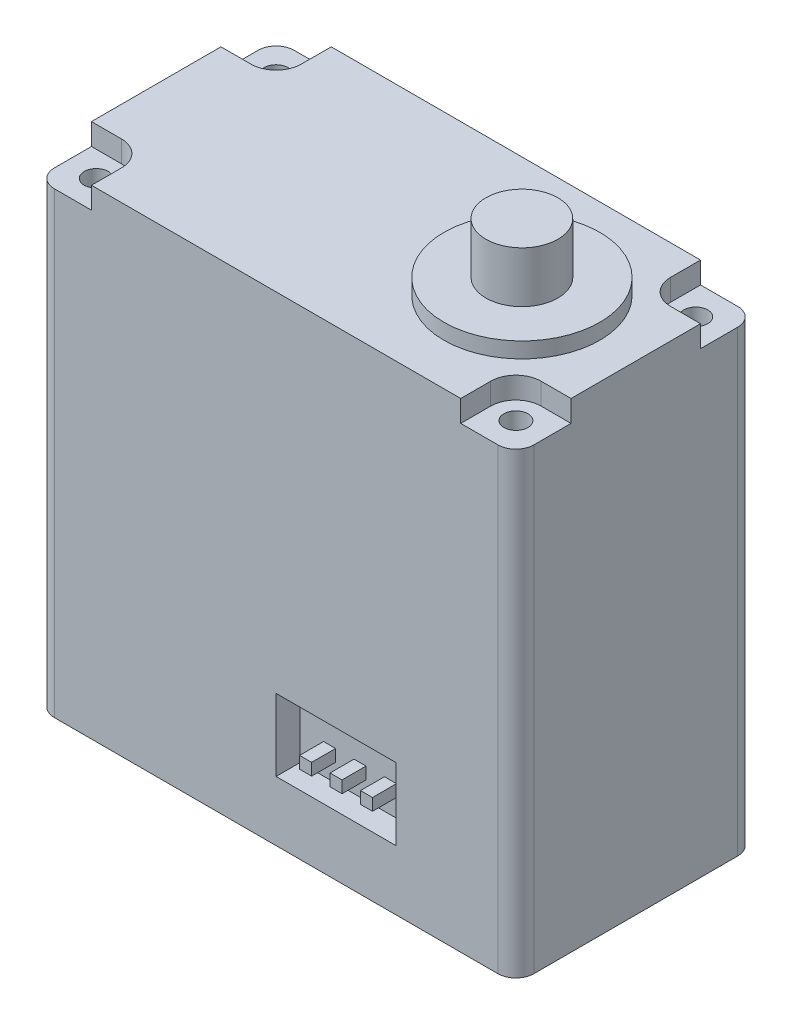
SolidWorks part; units mm, degrees
ref_plane "Спереди" through (0, 0, 0) normal (0, 0, 1) x (1, 0, 0)
ref_plane "Сверху" through (0, 0, 0) normal (0, 1, 0) x (1, 0, 0)
ref_plane "Справа" through (0, 0, 0) normal (1, 0, 0) x (0, 0, -1)
sketch "Эскиз1" plane through (0, 0, 0) normal (0, 1, 0) x (1, 0, 0)
  line L1 (-20, 10) -> (20, 10)
  line L2 (-20, 10) -> (-20, -10)
  line L3 (-20, -10) -> (20, -10)
  line L4 (20, 10) -> (20, -10)
  line L5 (-20, 10) -> (20, -10) construction
  line L6 (-20, -10) -> (20, 10) construction
  point P0 (0, 0)
  dimension "D1" = 20
  dimension "D2" = 40
extrude "Бобышка-Вытянуть1" add sketch "Эскиз1" along normal mid plane 40
fillet "Скругление1" radius 1.5 4 edges at (20, 0, -10) (-20, 0, -10) (-20, 0, 10) (20, 0, 10)
sketch "Эскиз2" plane through (0, 20, 0) normal (0, 1, 0) x (1, 0, 0)
  line L1 (-17.5, -7.5) -> (17.5, -7.5) construction
  line L2 (-17.5, -7.5) -> (-17.5, 7.5) construction
  line L3 (-17.5, 7.5) -> (17.5, 7.5) construction
  line L4 (17.5, -7.5) -> (17.5, 7.5) construction
  line L5 (-17.5, -7.5) -> (17.5, 7.5) construction
  line L6 (-17.5, 7.5) -> (17.5, -7.5) construction
  circle A1 centre (17.5, 7.5) radius 1
  circle A2 centre (17.5, -7.5) radius 1
  circle A3 centre (-17.5, -7.5) radius 1
  circle A4 centre (-17.5, 7.5) radius 1
  point P0 (0, 0)
  dimension "D3" = 2
  dimension "D1" = 35
  dimension "D2" = 15
extrude "Вырез-Вытянуть1" cut sketch "Эскиз2" against normal through all
sketch "Эскиз3" plane through (0, 20, 0) normal (0, 1, 0) x (1, 0, 0)
  line L0 (-21.4459, 5.4) -> (-15.4, 5.4)
  line L1 (-15.4, 5.4) -> (-15.4, 10.8358)
  line L2 (0, -50) -> (0, 50) construction
  line L3 (21.4459, 5.4) -> (15.4, 5.4)
  line L4 (15.4, 5.4) -> (15.4, 10.8358)
  line L5 (-50, 0) -> (50, 0) construction
  line L6 (-15.4, -5.4) -> (-15.4, -10.8358)
  line L7 (-21.4459, -5.4) -> (-15.4, -5.4)
  line L8 (21.4459, -5.4) -> (15.4, -5.4)
  line L9 (15.4, -5.4) -> (15.4, -10.8358)
  line L14 (20, -8.5) -> (20, 8.5)
  line L15 (18.5, 10) -> (-18.5, 10)
  line L16 (-20, 8.5) -> (-20, -8.5)
  line L17 (-18.5, -10) -> (18.5, -10)
  line L18 (20, -8.5) -> (20, 8.5)
  line L19 (18.5, 10) -> (-18.5, 10)
  line L20 (-20, 8.5) -> (-20, -8.5)
  line L21 (-18.5, -10) -> (18.5, -10)
  circle A0 centre (-17.5, 7.5) radius 2.1
  circle A1 centre (17.5, 7.5) radius 2.1
  circle A2 centre (17.5, -7.5) radius 2.1
  circle A3 centre (-17.5, -7.5) radius 2.1
  circle A5 centre (17.5, 7.5) radius 1 construction
  arc A10 (20, 8.5) -> (18.5, 10) centre (18.5, 8.5) ccw
  arc A11 (-18.5, 10) -> (-20, 8.5) centre (-18.5, 8.5) ccw
  arc A12 (-20, -8.5) -> (-18.5, -10) centre (-18.5, -8.5) ccw
  arc A13 (18.5, -10) -> (20, -8.5) centre (18.5, -8.5) ccw
  arc A14 (20, 8.5) -> (18.5, 10) centre (18.5, 8.5) ccw
  arc A15 (-18.5, 10) -> (-20, 8.5) centre (-18.5, 8.5) ccw
  arc A16 (-20, -8.5) -> (-18.5, -10) centre (-18.5, -8.5) ccw
  arc A17 (18.5, -10) -> (20, -8.5) centre (18.5, -8.5) ccw
  circle M19 centre (-17.5, -7.5) radius 1
  circle M20 centre (17.5, -7.5) radius 1
  circle M21 centre (17.5, 7.5) radius 1
  circle M22 centre (-17.5, 7.5) radius 1
  line M23 (20, -8.5) -> (20, 8.5)
  arc M24 (20, 8.5) -> (18.5, 10) centre (18.5, 8.5) ccw
  line M25 (18.5, 10) -> (-18.5, 10)
  arc M26 (-18.5, 10) -> (-20, 8.5) centre (-18.5, 8.5) ccw
  line M27 (-20, 8.5) -> (-20, -8.5)
  arc M28 (-20, -8.5) -> (-18.5, -10) centre (-18.5, -8.5) ccw
  line M29 (-18.5, -10) -> (18.5, -10)
  arc M30 (18.5, -10) -> (20, -8.5) centre (18.5, -8.5) ccw
  dimension "D1" = 4.2
  dimension "D4" = 0
  dimension "D2" = 2
  dimension "D3" = 2
extrude "Вырез-Вытянуть2" cut sketch "Эскиз3" against normal blind 1.8 contours A0 M22 | A0 L1 L0 M25 M26 M27 | A3 M19 | A3 L7 L6 M27 M28 M29 | A2 L9 L8 M29 M30 M23 | A2 M20 | A1 L3 L4 M23 M24 M25 | A1 M21
sketch "Эскиз4" plane through (0, 20, 0) normal (0, 1, 0) x (1, 0, 0)
  line L0 (20, -5.4) -> (20, 5.4) construction
  circle A0 centre (10.5, 0) radius 6.5
  point P4 (4, 0)
  dimension "D1" = 13
  dimension "D2" = 16
extrude "Бобышка-Вытянуть2" add sketch "Эскиз4" along normal blind 1.3
sketch "Эскиз5" plane through (0, 21.3, 0) normal (0, 1, 0) x (1, 0, 0)
  circle A0 centre (10.5, 0) radius 3
  circle A1 centre (10.5, 0) radius 6.5 construction
  dimension "D1" = 6
extrude "Бобышка-Вытянуть3" add sketch "Эскиз5" along normal blind 4.25
mirror "Зеркальное отражение1" about plane through (0, 0, 0) normal (0, 1, 0) of "Бобышка-Вытянуть3", "Бобышка-Вытянуть2"
sketch "Эскиз6" plane through (0, 0, 10) normal (0, 0, 1) x (1, 0, 0)
  line L0 (-18.5, -20) -> (18.5, -20) construction
  line L1 (0, -9) -> (10, -9)
  line L2 (0, -9) -> (0, -15)
  line L3 (0, -15) -> (10, -15)
  line L4 (10, -9) -> (10, -15)
  line L5 (20, 18.2) -> (20, -20) construction
  dimension "D1" = 6
  dimension "D2" = 10
  dimension "D3" = 5
  dimension "D4" = 10
extrude "Вырез-Вытянуть3" cut sketch "Эскиз6" against normal blind 2
sketch "Эскиз7" plane through (0, 0, 8) normal (0, 0, 1) x (1, 0, 0)
  line L1 (4.5, -12.5) -> (5.5, -12.5)
  line L2 (4.5, -12.5) -> (4.5, -13.5)
  line L3 (4.5, -13.5) -> (5.5, -13.5)
  line L4 (5.5, -12.5) -> (5.5, -13.5)
  line L5 (10, -9) -> (0, -9) construction
  line L6 (0, -15) -> (10, -15) construction
  line L7 (7.04, -12.5) -> (8.04, -12.5)
  line L8 (7.04, -12.5) -> (7.04, -13.5)
  line L9 (7.04, -13.5) -> (8.04, -13.5)
  line L10 (8.04, -12.5) -> (8.04, -13.5)
  line L11 (4.5, -12.5) -> (5.5, -12.5)
  line L12 (4.5, -12.5) -> (4.5, -13.5)
  line L13 (4.5, -13.5) -> (5.5, -13.5)
  line L14 (5.5, -12.5) -> (5.5, -13.5)
  line L15 (1.96, -12.5) -> (2.96, -12.5)
  line L16 (1.96, -12.5) -> (1.96, -13.5)
  line L17 (1.96, -13.5) -> (2.96, -13.5)
  line L18 (2.96, -12.5) -> (2.96, -13.5)
  point P6 (5, -12.5)
  point P7 (5, -9)
  dimension "D1" = 1
  dimension "D2" = 1.5
  dimension "D5" = 1.54
  dimension "D6" = 1.54
  dimension "D3" = 2
  dimension "D4" = 2
extrude "Бобышка-Вытянуть4" add sketch "Эскиз7" along normal blind 2 contours L18 L15 L16 L17 | L4 L1 L2 L3 | L10 L7 L8 L9
